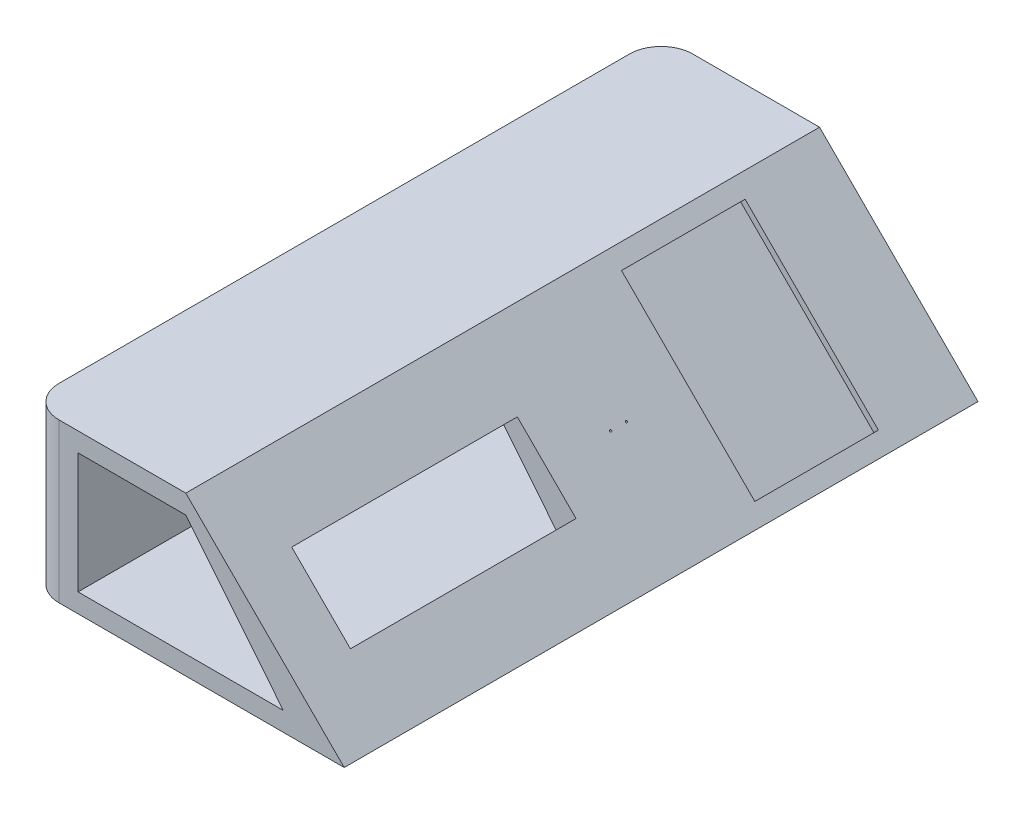
SolidWorks part; units mm, degrees
other "Markup1"
sketch "Sketch8" plane through (100, 50, 0) normal (0.7791, 0.5409, -0.3169) x (-0.216, -0.243, -0.9457)
material "Acrylic (Medium-high impact)"
ref_plane "Front Plane" through (0, 0, 0) normal (0, 0, 1) x (1, 0, 0)
ref_plane "Top Plane" through (0, 0, 0) normal (0, 1, 0) x (1, 0, 0)
ref_plane "Right Plane" through (0, 0, 0) normal (1, 0, 0) x (0, 0, -1)
sketch "Sketch1" plane through (0, 0, 0) normal (0, 0, 1) x (1, 0, 0)
  line L0 (0, 0) -> (100, 0)
  line L1 (0, 0) -> (0, 50)
  line L2 (0, 50) -> (50, 50)
  line L3 (50, 50) -> (100, 0)
  dimension "D1" = 100
  dimension "D2" = 50
  dimension "D3" = 45
extrude "Boss-Extrude1" add sketch "Sketch1" along normal blind 200
fillet "Fillet1" radius 10 2 edges at (0, 25, 0) (0, 25, 200)
sketch "Sketch2" plane through (50, 50, 0) normal (0.7071, 0.7071, 0) x (0, 0, -1)
  line L3 (-66.4623, -5.6053) -> (-27.4623, -5.6053)
  line L4 (-66.4623, -5.6053) -> (-66.4623, -65.1053)
  line L5 (-66.4623, -65.1053) -> (-27.4623, -65.1053)
  line L6 (-27.4623, -5.6053) -> (-27.4623, -65.1053)
  line L7 (-66.4623, -5.6053) -> (-27.4623, -65.1053) construction
  line L8 (-66.4623, -65.1053) -> (-27.4623, -5.6053) construction
  point P4 (-46.9623, -35.3553)
  dimension "D1" = 39
  dimension "D2" = 59.5
extrude "Cut-Extrude1" cut sketch "Sketch2" against normal blind 2 contours L3 L6 L5 L4
sketch "Sketch3" plane through (50, 50, 0) normal (0.7071, 0.7071, 0) x (0, 0, -1)
  line L4 (-182.3111, -22.2553) -> (-111.1111, -22.2553)
  line L5 (-182.3111, -22.2553) -> (-182.3111, -48.4553)
  line L6 (-182.3111, -48.4553) -> (-111.1111, -48.4553)
  line L7 (-111.1111, -22.2553) -> (-111.1111, -48.4553)
  line L8 (-182.3111, -22.2553) -> (-111.1111, -48.4553) construction
  line L9 (-182.3111, -48.4553) -> (-111.1111, -22.2553) construction
  point P6 (-146.7111, -35.3553)
  dimension "D1" = 71.2
  dimension "D2" = 26.2
extrude "Cut-Extrude2" cut sketch "Sketch3" against normal blind 10
sketch "Sketch6" plane through (0, 0, 200) normal (0, 0, 1) x (1, 0, 0)
  line L1 (10, 0) -> (100, 0) construction
  line L2 (50, 44) -> (80.7718, 6)
  line L3 (80.7718, 6) -> (16, 6)
  line L4 (16, 6) -> (16, 44)
  line L5 (16, 44) -> (50, 44)
  line L7 (100, 0) -> (50, 50) construction
  line L8 (10, 50) -> (10, 0) construction
  dimension "D2" = 6
  dimension "D3" = 6
  dimension "D4" = 6
  dimension "D5" = 51
extrude "Cut-Extrude4" cut sketch "Sketch6" against normal blind 215
sketch "Sketch10" plane through (50, 50, 0) normal (0.7071, 0.7071, 0) x (0, 0, -1)
  circle A0 centre (-90.9367, -35.3553) radius 0.3
  circle A1 centre (-85.9367, -35.3553) radius 0.3
  dimension "D1" = 0.6
  dimension "D2" = 5
extrude "Cut-Extrude5" cut sketch "Sketch10" against normal blind 10
